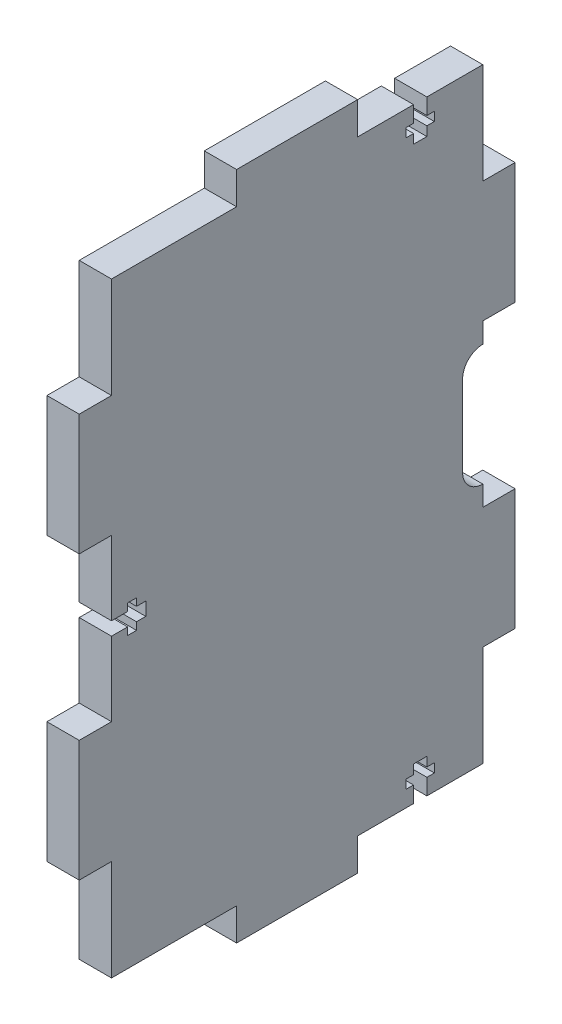
SolidWorks part; units mm, degrees
material "Acrylic (Medium-high impact)"
ref_plane "Front Plane" through (0, 0, 0) normal (0, 0, 1) x (1, 0, 0)
ref_plane "Top Plane" through (0, 0, 0) normal (0, 1, 0) x (1, 0, 0)
ref_plane "Right Plane" through (0, 0, 0) normal (1, 0, 0) x (0, 0, -1)
sketch "Sketch1" plane through (0, 0, 0) normal (1, 0, 0) x (0, 0, -1)
  line L1 (0, 0) -> (92, 0)
  line L2 (0, 0) -> (0, 150)
  line L3 (0, 150) -> (92, 150)
  line L4 (92, 0) -> (92, 150)
  dimension "D1" = 92
  dimension "D2" = 150
extrude "Boss-Extrude1" add sketch "Sketch1" along normal blind 8
sketch "Sketch2" plane through (0, 0, 0) normal (-1, 0, 0) x (0, 0, 1)
  line L0 (-92, 150) -> (0, 150) construction
  line L1 (-61, 150) -> (-31, 150)
  line L2 (-61, 150) -> (-61, 158)
  line L3 (-61, 158) -> (-31, 158)
  line L4 (-31, 150) -> (-31, 158)
  line L5 (-46, 150) -> (-46, 0) construction
  line L6 (0, 0) -> (-92, 0) construction
  line L7 (-92, 75) -> (0, 75) construction
  line L8 (-92, 0) -> (-92, 150) construction
  line L9 (0, 150) -> (0, 0) construction
  line L10 (-31, 0) -> (-31, -8)
  line L11 (-61, -8) -> (-31, -8)
  line L12 (-61, 0) -> (-61, -8)
  line L13 (-61, 0) -> (-31, 0)
  line L14 (8, 25) -> (8, 55)
  line L15 (0, 125) -> (8, 125)
  line L16 (0, 125) -> (0, 95)
  line L17 (0, 95) -> (8, 95)
  line L18 (8, 125) -> (8, 95)
  line L19 (0, 55) -> (8, 55)
  line L20 (0, 25) -> (0, 55)
  line L21 (0, 25) -> (8, 25)
  line L22 (-92, 25) -> (-100, 25)
  line L23 (-92, 25) -> (-92, 55)
  line L24 (-92, 55) -> (-100, 55)
  line L25 (-100, 125) -> (-100, 95)
  line L26 (-92, 95) -> (-100, 95)
  line L27 (-92, 125) -> (-92, 95)
  line L28 (-92, 125) -> (-100, 125)
  line L29 (-100, 25) -> (-100, 55)
  point P6 (-46, 158)
  point P21 (-46, -8)
  point P26 (8, 110)
  point P33 (8, 40)
  point P42 (-100, 40)
  point P43 (-100, 110)
  dimension "D1" = 30
  dimension "D2" = 8
  dimension "D3" = 30
  dimension "D4" = 8
  dimension "D5" = 25
extrude "Boss-Extrude2" add sketch "Sketch2" against normal blind 8
sketch "Sketch4" plane through (8, 0, 0) normal (1, 0, 0) x (0, 0, -1)
  line L0 (92, 85) -> (92, 65) construction
  line L1 (92, 55) -> (92, 95) construction
  line L2 (76.5, 0) -> (76.5, 150) construction
  line L3 (61, 0) -> (92, 0) construction
  line L4 (0, 75) -> (92, 75) construction
  line L5 (0, 95) -> (0, 55) construction
  line L6 (97, 85) -> (97, 65)
  line L7 (87, 85) -> (87, 65)
  line L8 (0, 76.65) -> (4, 76.65)
  line L9 (4, 76.65) -> (4, 78.5)
  line L10 (4, 78.5) -> (6.2, 78.5)
  line L11 (6.2, 78.5) -> (6.2, 76.65)
  line L12 (6.2, 76.65) -> (8.5, 76.65)
  line L13 (8.5, 76.65) -> (8.5, 73.35)
  line L14 (6.2, 73.35) -> (8.5, 73.35)
  line L15 (6.2, 71.5) -> (6.2, 73.35)
  line L16 (4, 71.5) -> (6.2, 71.5)
  line L17 (4, 73.35) -> (4, 71.5)
  line L18 (0, 73.35) -> (4, 73.35)
  line L19 (0, 76.65) -> (0, 73.35)
  line L20 (92, 150) -> (61, 150) construction
  line L21 (78.15, 0) -> (78.15, 4)
  line L22 (78.15, 4) -> (80, 4)
  line L23 (80, 4) -> (80, 6.2)
  line L24 (80, 6.2) -> (78.15, 6.2)
  line L25 (78.15, 6.2) -> (78.15, 8.5)
  line L26 (78.15, 8.5) -> (74.85, 8.5)
  line L27 (74.85, 6.2) -> (74.85, 8.5)
  line L28 (73, 6.2) -> (74.85, 6.2)
  line L29 (73, 4) -> (73, 6.2)
  line L30 (74.85, 4) -> (73, 4)
  line L31 (74.85, 0) -> (74.85, 4)
  line L32 (74.85, 0) -> (78.15, 0)
  line L33 (74.85, 150) -> (78.15, 150)
  line L34 (74.85, 150) -> (74.85, 146)
  line L35 (74.85, 146) -> (73, 146)
  line L36 (73, 146) -> (73, 143.8)
  line L37 (73, 143.8) -> (74.85, 143.8)
  line L38 (74.85, 143.8) -> (74.85, 141.5)
  line L39 (78.15, 141.5) -> (74.85, 141.5)
  line L40 (78.15, 143.8) -> (78.15, 141.5)
  line L41 (80, 143.8) -> (78.15, 143.8)
  line L42 (80, 146) -> (80, 143.8)
  line L43 (78.15, 146) -> (80, 146)
  line L44 (78.15, 150) -> (78.15, 146)
  arc A1 (97, 85) -> (87, 85) centre (92, 85) ccw
  arc A2 (87, 65) -> (97, 65) centre (92, 65) ccw
  point P12 (92, 75)
  point P17 (92, 75)
  point P23 (8.5, 75)
  point P41 (76.5, 8.5)
  point P58 (76.5, 141.5)
  dimension "D3" = 5
  dimension "D1" = 3.3
  dimension "D2" = 20
  dimension "D4" = 7
  dimension "D5" = 4
  dimension "D6" = 2.2
  dimension "D7" = 2.3
  dimension "D8" = 3.3
  dimension "D9" = 7
  dimension "D10" = 4
  dimension "D11" = 2.2
  dimension "D12" = 2.3
extrude "Cut-Extrude2" cut sketch "Sketch4" against normal through all
